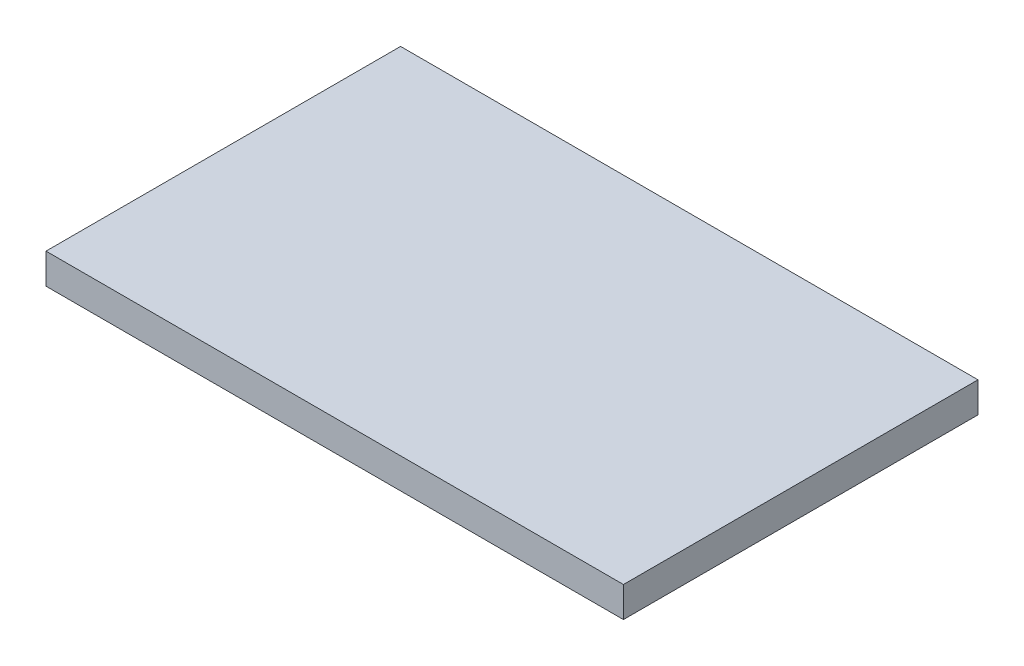
SolidWorks part; units mm, degrees
ref_plane "Спереди" through (0, 0, 0) normal (0, 0, 1) x (1, 0, 0)
ref_plane "Сверху" through (0, 0, 0) normal (0, 1, 0) x (1, 0, 0)
ref_plane "Справа" through (0, 0, 0) normal (1, 0, 0) x (0, 0, -1)
sketch "Эскиз1" plane through (0, 0, 0) normal (0, 1, 0) x (1, 0, 0)
  line L1 (0, 0) -> (570, 0)
  line L2 (0, 0) -> (0, 350)
  line L3 (0, 350) -> (570, 350)
  line L4 (570, 0) -> (570, 350)
extrude "Бобышка-Вытянуть1" add sketch "Эскиз1" along normal blind 30
